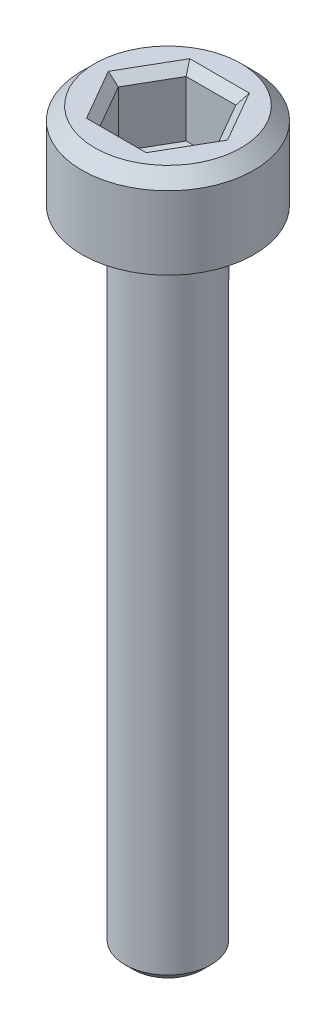
SolidWorks part; units mm, degrees
ref_plane "Front Plane" through (0, 0, 0) normal (0, 0, 1) x (1, 0, 0)
ref_plane "Top Plane" through (0, 0, 0) normal (0, 1, 0) x (1, 0, 0)
ref_plane "Right Plane" through (0, 0, 0) normal (1, 0, 0) x (0, 0, -1)
sketch "Sketch1" plane through (0, 0, 0) normal (0, 1, 0) x (1, 0, 0)
  circle A0 centre (0, 0) radius 2
  dimension "D1" = 4
extrude "Boss-Extrude1" add sketch "Sketch1" along normal blind 2
chamfer "Chamfer1" distance 0.3 angle 45 1 edges at (0, 2, 2)
sketch "Sketch2" plane through (0, 2, 0) normal (0, 1, 0) x (1, 0, 0)
  line L1 (1.1547, 0) -> (0.5774, 1)
  line L2 (0.5774, 1) -> (-0.5774, 1)
  line L3 (-0.5774, 1) -> (-1.1547, 0)
  line L4 (-1.1547, 0) -> (-0.5774, -1)
  line L5 (-0.5774, -1) -> (0.5774, -1)
  line L6 (0.5774, -1) -> (1.1547, 0)
  circle A0 centre (0, 0) radius 1 construction
  dimension "D1" = 2
extrude "Cut-Extrude1" cut sketch "Sketch2" against normal blind 1.5
chamfer "Chamfer2" distance 0.2 angle 45 6 edges at (0.866, 2, -0.5) (0.866, 2, 0.5) (0, 2, 1) (-0.866, 2, 0.5) (-0.866, 2, -0.5) (0, 2, -1)
sketch "Sketch3" plane through (0, 0, 0) normal (0, -1, 0) x (1, 0, 0)
  circle A0 centre (0, 0) radius 1
  dimension "D1" = 2
extrude "Boss-Extrude2" add sketch "Sketch3" along normal blind 15
chamfer "Chamfer3" distance 0.2 angle 45 1 edges at (0, -15, -1)
